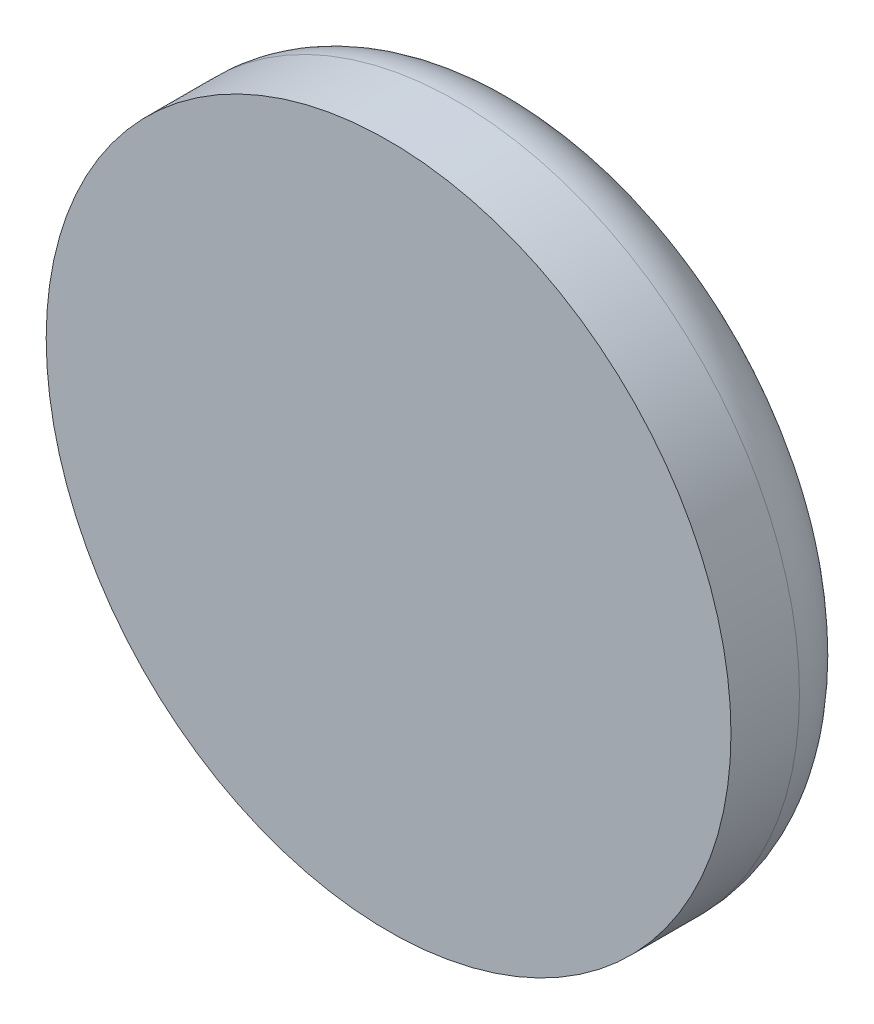
SolidWorks part; units mm, degrees
ref_plane "Front Plane" through (0, 0, 0) normal (0, 0, 1) x (1, 0, 0)
ref_plane "Top Plane" through (0, 0, 0) normal (0, 1, 0) x (1, 0, 0)
ref_plane "Right Plane" through (0, 0, 0) normal (1, 0, 0) x (0, 0, -1)
ref_plane "Plane1" through (0, 15.153, 0) normal (0, 1, 0) x (1, 0, 0)
sketch "Sketch1" plane through (0, 15.153, 0) normal (0, 1, 0) x (1, 0, 0)
  line L0 (1, 4.9467) -> (0, 4.9467)
  line L1 (0, 4.9467) -> (0, 4.3467)
  line L2 (0, 4.3467) -> (5, 4.3467)
  line L3 (5, 4.3467) -> (5, 5.3467)
  line L4 (4, 6.3467) -> (1, 6.3467)
  line L5 (1, 6.3467) -> (1, 4.9467)
  line L6 (0, 6.3467) -> (0, 4.3467) construction
  arc A0 (5, 5.3467) -> (4, 6.3467) centre (4, 5.3467) ccw
revolve "Revolve1" add sketch "Sketch1" angle 360 about L6
